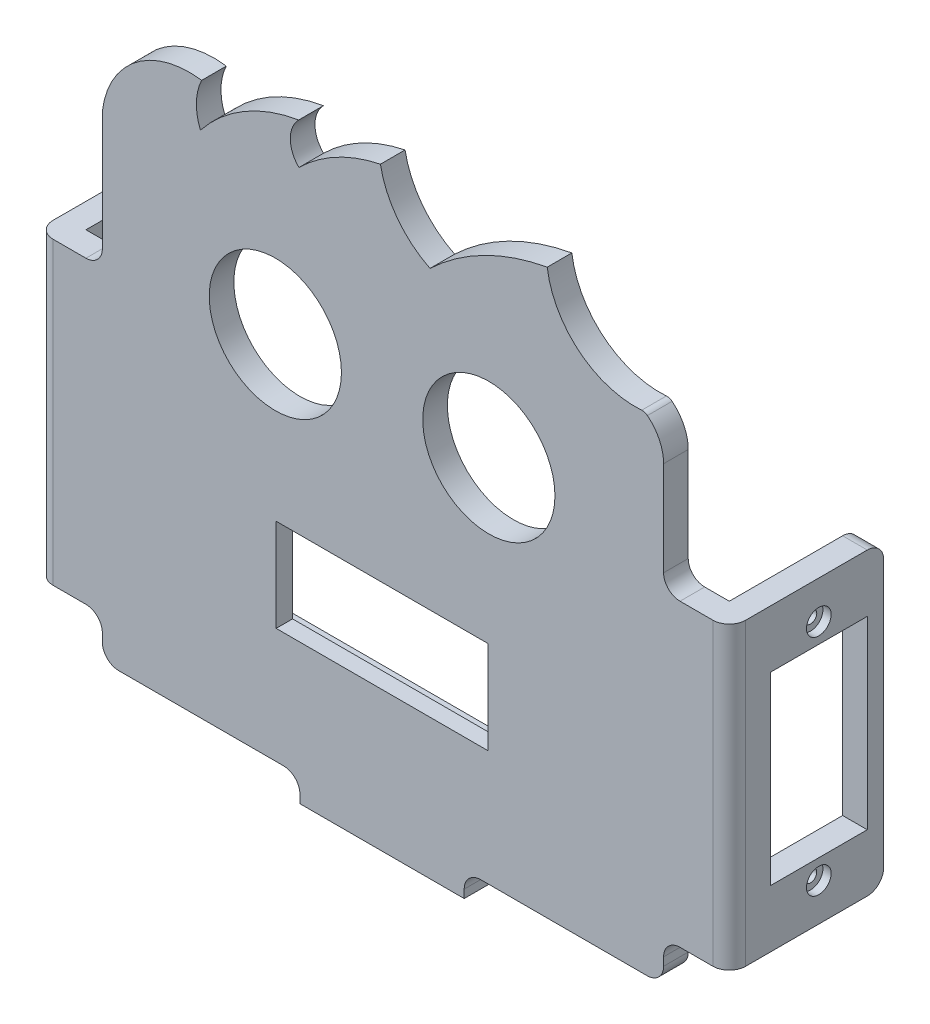
SolidWorks part; units mm, degrees
ref_plane "Alzado" through (0, 0, 0) normal (0, 0, 1) x (1, 0, 0)
ref_plane "Planta" through (0, 0, 0) normal (0, 1, 0) x (1, 0, 0)
ref_plane "Vista lateral" through (0, 0, 0) normal (1, 0, 0) x (0, 0, -1)
sketch "Model" plane through (0, 0, 0) normal (0, 0, 1) x (1, 0, 0)
  line L0 (102.8708, -11.521) -> (102.8708, -48.021)
  line L1 (18.5271, -11.521) -> (18.5271, -48.021)
  line L2 (50.5898, -56.0212) -> (70.5898, -56.0212)
  line L3 (60.5898, -27.6769) -> (60.5898, -56.0212) construction
  line L4 (47.5898, -8.0207) -> (73.5898, -8.0207) construction
  line L5 (60.5898, -27.6769) -> (60.5898, -8.0207) construction
  line L6 (28.5271, -53.021) -> (48.5898, -53.0212)
  line L7 (72.5898, -53.021) -> (92.8708, -53.021)
  line L12 (96.8708, -11.521) -> (102.8708, -11.521)
  line L13 (102.8708, -48.021) -> (96.8708, -48.021)
  line L14 (18.5271, -11.521) -> (24.5271, -11.521)
  line L15 (18.5271, -48.021) -> (24.5271, -48.021)
  line L42 (73.4898, -38.9769) -> (73.4898, -27.6769)
  line L43 (73.4898, -27.6769) -> (47.6898, -27.6769)
  line L44 (47.6898, -27.6769) -> (47.6898, -38.9769)
  line L45 (47.6898, -38.9769) -> (73.4898, -38.9769)
  line L46 (26.5271, 4.938) -> (26.5271, -9.521)
  line L47 (94.8708, -9.521) -> (94.8708, 1.979)
  line L55 (94.8708, -51.021) -> (94.8708, -50.021)
  line L57 (70.5898, -55.021) -> (70.5898, -56.0212)
  line L87 (50.5898, -56.0212) -> (50.5898, -55.0212)
  line L89 (26.5271, -50.021) -> (26.5271, -51.021)
  arc A0 (96.8708, -11.521) -> (94.8708, -9.521) centre (96.8708, -9.521) cw
  arc A1 (94.8708, -50.021) -> (96.8708, -48.021) centre (96.8708, -50.021) cw
  arc A2 (26.5271, -50.021) -> (24.5271, -48.021) centre (24.5271, -50.021) ccw
  arc A3 (24.5271, -11.521) -> (26.5271, -9.521) centre (24.5271, -9.521) ccw
  arc A4 (70.5898, -55.021) -> (72.5898, -53.021) centre (72.5898, -55.021) cw
  arc A5 (50.5898, -55.0212) -> (48.5898, -53.0212) centre (48.5898, -55.0212) ccw
  circle A31 centre (73.5898, -8.0207) radius 8.05
  circle A32 centre (47.5898, -8.0207) radius 8.05
  arc A35 (38.6183, 14.2825) -> (26.5271, 4.938) centre (37.1049, 3.7459) ccw
  arc A36 (38.6183, 14.2825) -> (38.4712, 8.9598) centre (44.4932, 11.4568) ccw
  arc A37 (50.4388, 16.015) -> (38.4712, 8.9598) centre (53.6269, -3.0705) ccw
  arc A38 (50.4388, 16.015) -> (50.4619, 11.0151) centre (52.9503, 13.5266) ccw
  arc A39 (60.3874, 16.325) -> (50.4619, 11.0151) centre (64.38, -3.0696) ccw
  arc A40 (60.3874, 16.325) -> (66.4243, 8.3528) centre (71.3781, 18.3757) ccw
  arc A41 (80.6979, 15.6221) -> (66.4243, 8.3528) centre (85.7044, -11.8565) ccw
  arc A42 (80.6979, 15.6221) -> (92.2046, 6.289) centre (91.4116, 17.0711) ccw
  arc A43 (92.9023, 6.0728) -> (92.2046, 6.289) centre (92.2779, 5.2917) ccw
  arc A44 (94.8708, 1.979) -> (92.9023, 6.0728) centre (89.6297, 1.979) ccw
  arc A48 (92.8708, -53.021) -> (94.8708, -51.021) centre (92.8708, -51.021) ccw
  arc A65 (26.5271, -51.021) -> (28.5271, -53.021) centre (28.5271, -51.021) ccw
  dimension "D1" = 2
  dimension "D2" = 2
  dimension "D3" = 2
  dimension "D4" = 2
  dimension "D6" = 2
  dimension "D5" = 20
extrude "Saliente-Extruir1" add sketch "Model" along normal blind 3
sketch "Croquis2" plane through (0, 0, 0) normal (0, 0, -1) x (-1, 0, 0)
  line L0 (-73.4898, -27.6769) -> (-47.6898, -27.6769) construction
  line L1 (-80.9398, -39.3769) -> (-42.6398, -39.3769)
  line L2 (-80.9398, -39.3769) -> (-80.9398, -27.2769)
  line L3 (-80.9398, -27.2769) -> (-42.6398, -27.2769)
  line L4 (-42.6398, -39.3769) -> (-42.6398, -27.2769)
  line L5 (-47.6898, -27.6769) -> (-47.6898, -38.9769) construction
  dimension "D1" = 38.3
  dimension "D2" = 12.1
  dimension "D3" = 0.4
  dimension "D4" = 5.05
extrude "Cortar-Extruir1" cut sketch "Croquis2" against normal blind 1
sketch "Croquis3" plane through (0, 0, 0) normal (0, 0, -1) x (-1, 0, 0)
  line L1 (-102.8708, -11.521) -> (-99.8708, -11.521)
  line L2 (-102.8708, -11.521) -> (-102.8708, -48.021)
  line L3 (-102.8708, -48.021) -> (-99.8708, -48.021)
  line L4 (-99.8708, -11.521) -> (-99.8708, -48.021)
  dimension "D1" = 3
extrude "Saliente-Extruir2" add sketch "Croquis3" along normal blind 15.8
sketch "Croquis4" plane through (102.8708, 0, 0) normal (1, 0, 0) x (0, 0, -1)
  line L0 (2, -18.521) -> (2, -41.021)
  line L1 (2, -41.021) -> (13.8, -41.021)
  line L2 (13.8, -41.021) -> (13.8, -18.521)
  line L3 (13.8, -18.521) -> (2, -18.521)
  line L4 (7.9, -43.421) -> (7.9, -16.121) construction
  line L5 (15.8, -11.521) -> (15.8, -48.021) construction
  line L6 (-3, -11.521) -> (15.8, -11.521) construction
  circle A0 centre (7.9, -43.421) radius 0.75
  circle A1 centre (7.9, -16.121) radius 0.75
  dimension "D1" = 2.4
  dimension "D2" = 11.8
  dimension "D3" = 22.5
  dimension "D4" = 2.4
  dimension "D5" = 5.9
  dimension "D6" = 2
  dimension "D7" = 7
extrude "Cortar-Extruir2" cut sketch "Croquis4" against normal blind 3
sketch "Croquis5" plane through (102.8708, 0, 0) normal (1, 0, 0) x (0, 0, -1)
  circle A0 centre (7.9, -16.121) radius 1.5
  circle A1 centre (7.9, -43.421) radius 1.5
extrude "Cortar-Extruir3" cut sketch "Croquis5" against normal blind 1
fillet "Redondeo1" radius 2 2 edges at (101.3708, -48.021, -15.8) (101.3708, -11.521, -15.8)
ref_plane "Plano1" through (60.7008, 0, 0) normal (1, 0, 0) x (0, 0, -1)
mirror "Simetría1" about plane through (60.7008, 0, 0) normal (1, 0, 0) of "Redondeo1", "Saliente-Extruir2", "Cortar-Extruir2", "Cortar-Extruir3"
fillet "Redondeo2" radius 2 2 edges at (102.8708, -29.771, 3) (18.5271, -29.771, 3)
sketch "Croquis6" plane through (0, 0, 0) normal (0, 0, -1) x (-1, 0, 0)
  line L1 (-70.5898, -56.0212) -> (-50.5898, -56.0212)
  line L2 (-70.5898, -56.0212) -> (-70.5898, -53.0212)
  line L3 (-70.5898, -53.0212) -> (-50.5898, -53.0212)
  line L4 (-50.5898, -56.0212) -> (-50.5898, -53.0212)
  dimension "D1" = 3
extrude "Saliente-Extruir3" add sketch "Croquis6" along normal blind 8
sketch "Croquis7" plane through (0, -53.0212, 0) normal (0, 1, 0) x (1, 0, 0)
  line L0 (60.5898, 8) -> (60.5898, 0) construction
  line L1 (50.5898, 8) -> (70.5898, 8) construction
  line L2 (50.5898, 0) -> (70.5898, 0) construction
  circle A0 centre (66.5898, 3.5) radius 1.5
  circle A1 centre (54.5898, 3.5) radius 1.5
  dimension "D1" = 6
  dimension "D2" = 3.5
extrude "Cortar-Extruir4" cut sketch "Croquis7" against normal blind 3
sketch "Croquis8" plane through (0, -53.0212, 0) normal (0, 1, 0) x (1, 0, 0)
  circle A0 centre (66.5898, 3.5) radius 2.25
  circle A1 centre (54.5898, 3.5) radius 2.25
extrude "Cortar-Extruir5" cut sketch "Croquis8" against normal blind 1
fillet "Redondeo3" radius 2 2 edges at (50.5898, -54.5212, -8) (70.5898, -54.5212, -8)
